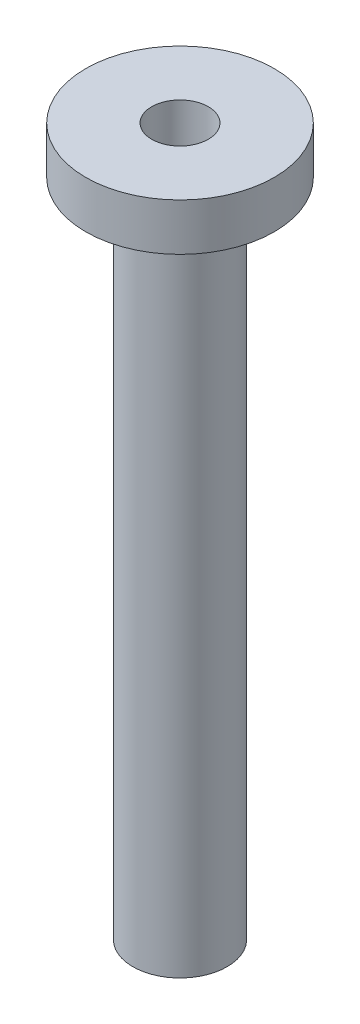
SolidWorks part; units mm, degrees
ref_plane "Front Plane" through (0, 0, 0) normal (0, 0, 1) x (1, 0, 0)
ref_plane "Top Plane" through (0, 0, 0) normal (0, 1, 0) x (1, 0, 0)
ref_plane "Right Plane" through (0, 0, 0) normal (1, 0, 0) x (0, 0, -1)
sketch "Sketch1" plane through (0, 0, 0) normal (0, 0, 1) x (1, 0, 0)
  line L0 (-3.81, 0) -> (-6.35, -2.54)
  line L1 (-6.35, -2.54) -> (-6.35, 86.36)
  line L2 (-10.9855, 86.36) -> (-12.7, 86.36)
  line L3 (-12.7, 86.36) -> (-12.7, 92.71)
  line L4 (-12.7, 92.71) -> (-3.81, 92.71)
  line L5 (-3.81, 92.71) -> (-3.81, 0)
  line L6 (0, 0) -> (0, 11.9708) construction
  line L7 (-6.35, 86.36) -> (-7.9375, 86.36)
  line L8 (-7.9375, 86.36) -> (-7.9375, 88.392)
  line L9 (-7.9375, 88.392) -> (-10.9855, 88.392)
  line L10 (-10.9855, 88.392) -> (-10.9855, 86.36)
  dimension "D1" = 3.81
  dimension "D2" = 6.35
  dimension "D3" = 88.9
  dimension "D4" = 6.35
  dimension "D5" = 6.35
  dimension "D6" = 45
  dimension "D7" = 3.048
  dimension "D8" = 2.032
  dimension "D9" = 1.5875
revolve "Revolve1" add sketch "Sketch1" angle 360 about L6
